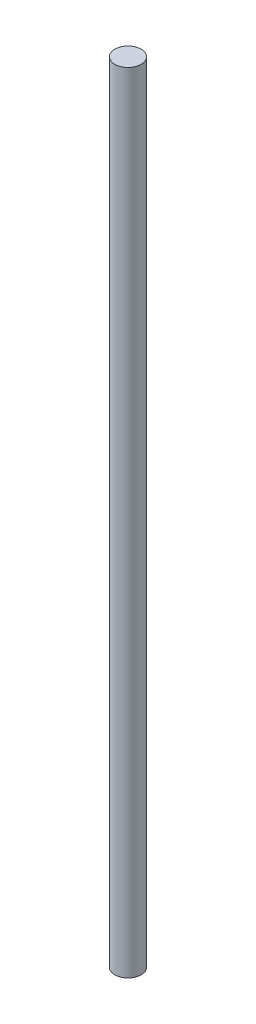
SolidWorks part; units mm, degrees
ref_plane "Front Plane" through (0, 0, 0) normal (0, 0, 1) x (1, 0, 0)
ref_plane "Top Plane" through (0, 0, 0) normal (0, 1, 0) x (1, 0, 0)
ref_plane "Right Plane" through (0, 0, 0) normal (1, 0, 0) x (0, 0, -1)
sketch "Croquis1" plane through (0, 0, 0) normal (0, 1, 0) x (1, 0, 0)
  circle A0 centre (0, 0) radius 0.25
  dimension "D1" = 0.5
extrude "Saliente-Extruir1" add sketch "Croquis1" along normal blind 15
